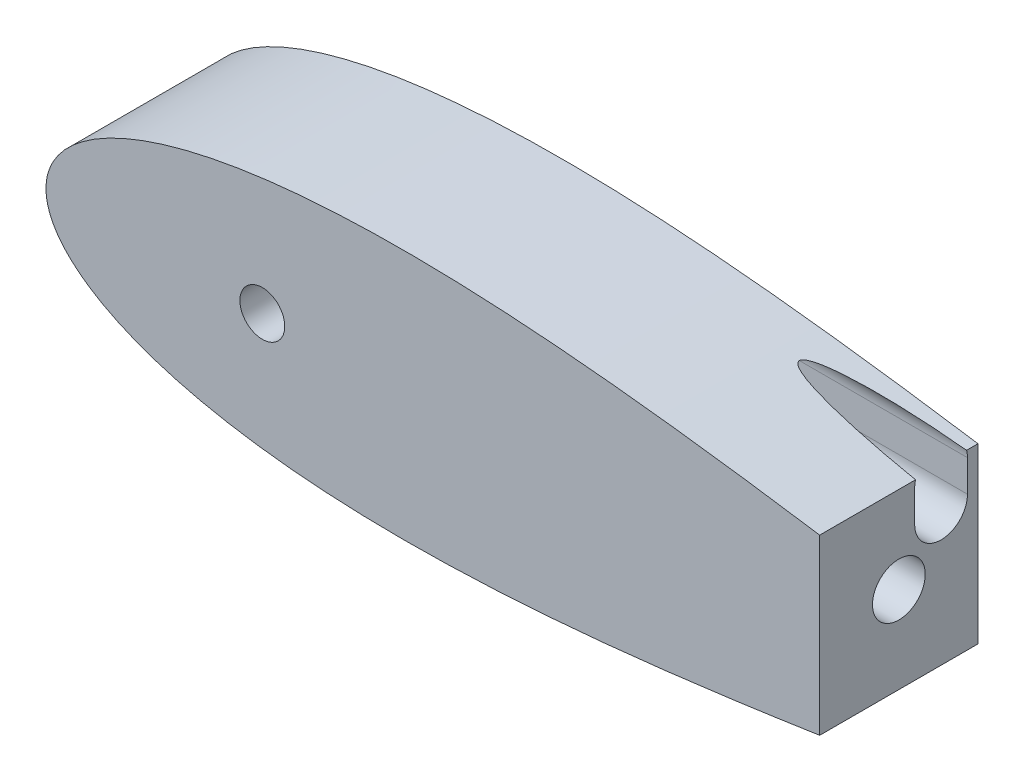
SolidWorks part; units mm, degrees
ref_plane "Front Plane" through (0, 0, 0) normal (0, 0, 1) x (1, 0, 0)
ref_plane "Top Plane" through (0, 0, 0) normal (0, 1, 0) x (1, 0, 0)
ref_plane "Right Plane" through (0, 0, 0) normal (1, 0, 0) x (0, 0, -1)
sketch "Sketch1" plane through (0, 0, 0) normal (0, 0, 1) x (1, 0, 0)
  line L0 (100, 0) -> (0, 0) construction
  line L1 (1.2169, -991.9959) -> (1.2169, 49008.0041) construction
  line L2 (93.345, 0) -> (114.935, 0) construction
  line L3 (125.634, 0) -> (131.6629, 0) construction
  line L4 (643.5991, 0) -> (643.5991, -1.016)
  line L9 (0, 0) -> (643.9668, 0)
  line L13 (460.661, 0) -> (473.361, 0)
  circle A0 centre (104.14, 0) radius 10.795 construction
  arc A1 (1.2169, -4.6585) -> (1.2169, 4.6585) centre (9.525, 0) cw
  arc A2 (641.5671, 0) -> (644.1071, 0) centre (642.8371, 0) ccw
  circle A4 centre (104.14, 0) radius 10.795
  circle A9 centre (40.64, 0) radius 12.7
  circle A14 centre (642.3793, 0) radius 1.5875 construction
  arc A15 (642.5108, -1.582) -> (642.5108, 1.582) centre (642.3793, 0) ccw
  spline S2 degree 3 poles (666.3448, -0.0547) (672.2538, 0) (666.3448, 0.0547) (662.8509, 0.2344) (656.505, 0.5436) (649.293, 1.0348) (640.4916, 1.7319) (630.4138, 2.6634) (619.0141, 3.8493) (606.375, 5.3044) (592.5439, 7.0376) (577.5855, 9.0506) (561.5643, 11.3389) (544.5497, 13.8907) (526.6141, 16.6877) (507.8326, 19.7051) (488.2827, 22.9117) (468.0444, 26.2704) (447.1994, 29.739) (425.8316, 33.2703) (404.0263, 36.8132) (381.8707, 40.3133) (359.4533, 43.7135) (336.8645, 46.9554) (314.1962, 49.9798) (291.5418, 52.7277) (268.9963, 55.1412) (246.6566, 57.1646) (224.6209, 58.7452) (202.9892, 59.8341) (181.8631, 60.3875) (161.3458, 60.367) (141.542, 59.7399) (122.5581, 58.4818) (104.5023, 56.5743) (87.485, 54.0089) (71.6197, 50.7848) (57.0237, 46.9125) (43.8205, 42.415) (32.1416, 37.3322) (22.1291, 31.7315) (13.9324, 25.7264) (7.6896, 19.5132) (3.4631, 13.4204) (1.1063, 7.9234) (0.1546, 3.5138) (-0.0622, 0) (0.1546, -3.5138) (1.1063, -7.9234) (3.4631, -13.4204) (7.6896, -19.5132) (13.9324, -25.7264) (22.1291, -31.7315) (32.1416, -37.3322) (43.8205, -42.415) (57.0237, -46.9125) (71.6197, -50.7848) (87.485, -54.0089) (104.5023, -56.5743) (122.5581, -58.4818) (141.542, -59.7399) (161.3458, -60.367) (181.8631, -60.3875) (202.9892, -59.8341) (224.6209, -58.7452) (246.6566, -57.1646) (268.9963, -55.1412) (291.5418, -52.7277) (314.1962, -49.9798) (336.8645, -46.9554) (359.4533, -43.7135) (381.8707, -40.3133) (404.0263, -36.8132) (425.8316, -33.2703) (447.1994, -29.739) (468.0444, -26.2704) (488.2827, -22.9117) (507.8326, -19.7051) (526.6141, -16.6877) (544.5497, -13.8907) (561.5643, -11.3389) (577.5855, -9.0506) (592.5439, -7.0376) (606.375, -5.3044) (619.0141, -3.8493) (630.4138, -2.6634) (640.4916, -1.7319) (649.293, -1.0348) (656.505, -0.5436) (662.8509, -0.2344) (666.3448, -0.0547) (672.2538, 0) (666.3448, 0.0547) knots -0.009667 -0.005395 -0.002168 0 0.002168 0.005395 0.009667 0.014967 0.021271 0.028553 0.036781 0.04592 0.055932 0.066773 0.078397 0.090755 0.103793 0.117456 0.131686 0.146422 0.1616 0.177156 0.193024 0.209135 0.225421 0.241812 0.258238 0.274629 0.290914 0.307025 0.322893 0.338448 0.353626 0.368361 0.38259 0.396253 0.40929 0.421647 0.43327 0.444109 0.454119 0.463255 0.471479 0.478755 0.485052 0.490344 0.49461 0.497833 0.5 0.502167 0.50539 0.509656 0.514948 0.521245 0.528521 0.536745 0.545881 0.555891 0.56673 0.578353 0.59071 0.603747 0.61741 0.631639 0.646374 0.661552 0.677107 0.692975 0.709086 0.725371 0.741762 0.758188 0.774579 0.790865 0.806976 0.822844 0.8384 0.853578 0.868314 0.882544 0.896207 0.909245 0.921603 0.933227 0.944068 0.95408 0.963219 0.971447 0.978729 0.985033 0.990333 0.994605 0.997832 1 1.002168 1.005395 1.009667 only from (670.56, 0) to (670.56, 0)
  point P2 (167.64, 0)
  point P8 (1.2169, -4.6585)
  point P10 (1.2169, 4.6585)
  point P28 (133.9182, 0)
  point P49 (130.0977, 0)
  point P59 (95.1064, 0)
  dimension "D2" = 21.59
  dimension "D3" = 1.016
  dimension "D4" = 1.27
  dimension "D8" = 25.4
  dimension "D9" = 63.5
  dimension "D10" = 3.175
  dimension "D6" = 63.5
extrude "Boss-Extrude1" add sketch "Sketch1" along normal blind 76.2 contours S2
sketch "Sketch3" plane through (0, 0, 76.2) normal (0, 0, 1) x (1, 0, 0)
  circle A0 centre (104.1392, 0) radius 10.795
  dimension "D1" = 21.59
extrude "Cut-Extrude2" cut sketch "Sketch3" against normal blind 76.2
sketch "Sketch4" plane through (0, 0, 76.2) normal (0, 0, 1) x (1, 0, 0)
sketch "Sketch6" plane through (0, 0, 0) normal (1, 0, 0) x (0, 0, -1)
  circle A0 centre (-20.32, 0) radius 6.35
  dimension "D1" = 12.7
  dimension "D2" = 20.32
extrude "Cut-Extrude3" cut sketch "Sketch6" against normal blind 0.0003 and the other way blind 53.34
sketch "Sketch7" plane through (0, 0, 0) normal (0, 0, -1) x (-1, 0, 0)
  circle A0 centre (-38.1, 0) radius 1.5875
  circle A1 centre (-50.8, 0) radius 1.5875
  dimension "D1" = 3.175
  dimension "D2" = 3.175
  dimension "D3" = 12.7
  dimension "D4" = 38.1
extrude "Cut-Extrude4" cut sketch "Sketch7" against normal blind 30.48
sketch "Sketch8" plane through (0, 0, 0) normal (0, 0, -1) x (-1, 0, 0)
  line L1 (-677.2433, 63.9901) -> (-372.4433, 63.9901)
  line L2 (-677.2433, 63.9901) -> (-677.2433, -63.0099)
  line L3 (-677.2433, -63.0099) -> (-372.4433, -63.0099)
  line L4 (-372.4433, 63.9901) -> (-372.4433, -63.0099)
  dimension "D1" = 127
  dimension "D2" = 372.4433
  dimension "D3" = 304.8
extrude "Cut-Extrude5" cut sketch "Sketch8" against normal blind 76.2
sketch "Sketch9" plane through (372.4433, 0, 0) normal (1, 0, 0) x (0, 0, -1)
  line L0 (0, -41.7363) -> (0, 41.7363) construction
  circle A0 centre (-38.1, 0) radius 12.7
  dimension "D1" = 25.4
  dimension "D2" = 38.1
extrude "Cut-Extrude6" cut sketch "Sketch9" against normal blind 101.6 contours A0
sketch "Sketch10" plane through (0, 0, 0) normal (0, 0, -1) x (-1, 0, 0)
  line L0 (-372.4433, -41.7363) -> (-372.4433, 41.7363) construction
  circle A0 centre (-343.8683, 0) radius 3.175
  circle A1 centre (-286.7183, 0) radius 3.175
  dimension "D1" = 57.15
  dimension "D2" = 28.575
  dimension "D3" = 6.35
  dimension "D4" = 6.35
extrude "Cut-Extrude7" cut sketch "Sketch10" against normal blind 57.15
sketch "Sketch11" plane through (0, 0, 0) normal (0, 0, -1) x (-1, 0, 0)
  circle A0 centre (-286.7183, 0) radius 5.08
  circle A1 centre (-343.8683, 0) radius 5.08
  dimension "D1" = 10.16
extrude "Cut-Extrude8" cut sketch "Sketch11" against normal blind 6.35
sketch "Sketch12" plane through (0, 0, 0) normal (0, 0, -1) x (-1, 0, 0)
  circle A0 centre (-38.1, 0) radius 3.175
  circle A1 centre (-50.8, 0) radius 3.175
  dimension "D1" = 6.35
  dimension "D2" = 6.35
extrude "Cut-Extrude9" cut sketch "Sketch12" against normal blind 6.35
sketch "Sketch13" plane through (372.4433, 0, 0) normal (1, 0, 0) x (0, 0, -1)
  line L0 (-17.78, 23.2323) -> (-17.78, 38.4723) construction
  line L1 (-30.48, 23.2323) -> (-30.48, 38.4723)
  line L2 (-5.08, 23.2323) -> (-5.08, 38.4723)
  line L3 (0, -41.7363) -> (0, 41.7363) construction
  line L4 (-76.2, -41.7363) -> (-76.2, 41.7363) construction
  arc A0 (-30.48, 23.2323) -> (-5.08, 23.2323) centre (-17.78, 23.2323) ccw
  arc A1 (-5.08, 38.4723) -> (-30.48, 38.4723) centre (-17.78, 38.4723) ccw
  point P2 (-17.78, 30.8523)
  dimension "D1" = 5.08
  dimension "D2" = 45.72
  dimension "D4" = 15.24
extrude "Cut-Extrude10" cut sketch "Sketch13" against normal blind 198.458
